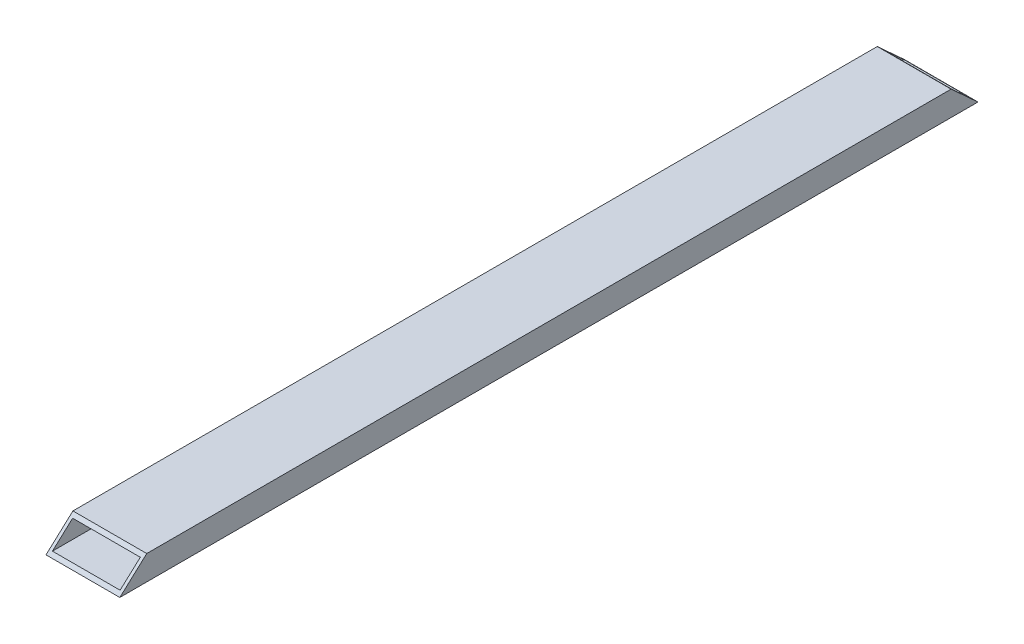
SolidWorks part; units mm, degrees
material "6063-T6"
ref_plane "Front Plane" through (0, 0, 0) normal (0, 0, 1) x (1, 0, 0)
ref_plane "Top Plane" through (0, 0, 0) normal (0, 1, 0) x (1, 0, 0)
ref_plane "Right Plane" through (0, 0, 0) normal (1, 0, 0) x (0, 0, -1)
sketch "Sketch1" plane through (0, 0, 0) normal (0, 0, 1) x (1, 0, 0)
  line L0 (-38.1, 0) -> (38.1, 0) construction
  line L1 (0, -12.7) -> (0, 12.7) construction
  line L2 (34.925, 0) -> (34.925, 9.525) construction
  line L3 (-38.1, -12.7) -> (38.1, -12.7) construction
  line L4 (-38.1, -12.7) -> (-38.1, 12.7) construction
  line L5 (-38.1, 12.7) -> (38.1, 12.7) construction
  line L6 (38.1, -12.7) -> (38.1, 12.7) construction
  line L7 (-38.1, -12.7) -> (38.1, 12.7) construction
  line L8 (-38.1, 12.7) -> (38.1, -12.7) construction
  line L9 (34.925, 9.525) -> (-34.925, 9.525) construction
  line L10 (-34.925, 9.525) -> (-34.925, -9.525) construction
  line L11 (-34.925, -9.525) -> (34.925, -9.525) construction
  line L12 (34.925, -9.525) -> (34.925, 0) construction
  point P0 (0, 0)
  point P4 (0, 0)
  point P9 (0, 0)
  point P10 (34.925, 0)
  point P13 (0, -9.525)
  point P14 (-34.925, 0)
  point P15 (0, 9.525)
  dimension "Width" = 76.2
  dimension "Wall Thickness" = 3.175
  dimension "Height" = 25.4
  dimension "D1" = 3.175
  dimension "D2" = 3.175
  dimension "D3" = 3.175
sketch "Sketch2" plane through (0, 0, 0) normal (1, 0, 0) x (0, 0, -1)
  line L0 (457.2, 12.7) -> (-457.2, 12.7) construction
  point P3 (-369.57, 12.7)
  point P5 (369.57, 12.7)
  point P7 (0, 12.7)
  dimension "D1" = 87.63
  dimension "D2" = 87.63
  dimension "Length" = 914.4
sketch "Sketch3" plane through (0, 0, 0) normal (0, 0, 1) x (1, 0, 0)
  line L1 (38.1, 12.7) -> (-38.1, 12.7)
  line L2 (-38.1, 12.7) -> (-38.1, -12.7)
  line L3 (-38.1, -12.7) -> (38.1, -12.7) construction
  line L4 (-38.1, -12.7) -> (38.1, -12.7)
  line L5 (38.1, -12.7) -> (38.1, 12.7)
  line L6 (-34.925, 9.525) -> (34.925, 9.525)
  line L7 (34.925, 9.525) -> (34.925, -9.525)
  line L8 (34.925, -9.525) -> (-34.925, -9.525)
  line L9 (-34.925, -9.525) -> (-34.925, 9.525)
extrude "Boss-Extrude1" add sketch "Sketch3" along normal mid plane 914.4
sketch "Sketch4" plane through (38.1, 0, 0) normal (1, 0, 0) x (0, 0, -1)
  line L0 (-457.2, -12.7) -> (457.2, -12.7) construction
  line L1 (442.9125, 12.7) -> (-442.9125, 12.7)
  line L2 (442.9125, 12.7) -> (442.9125, -12.7)
  line L3 (442.9125, -12.7) -> (-442.9125, -12.7)
  line L4 (-442.9125, 12.7) -> (-442.9125, -12.7)
  line L5 (442.9125, 12.7) -> (-442.9125, -12.7) construction
  line L6 (442.9125, -12.7) -> (-442.9125, 12.7) construction
  line L7 (0, 252.2904) -> (0, -470.7583) construction
  line L8 (-415.1312, 12.7) -> (-442.9125, -12.7)
  line L9 (415.1312, 12.7) -> (442.9125, -12.7)
  point P0 (0, 0)
  point P9 (-415.1312, 12.7)
  line M7 (457.2, -12.7) -> (457.2, 12.7)
  line M8 (457.2, 12.7) -> (-457.2, 12.7)
  line M9 (-457.2, 12.7) -> (-457.2, -12.7)
  line M10 (-457.2, -12.7) -> (457.2, -12.7)
  dimension "D1" = 885.825
  dimension "D2" = 415.1313
extrude "Cut-Extrude1" cut sketch "Sketch4" against normal through all contours L4 M8 M9 M10 | L8 L1 L4 | L2 M8 M10 M7 | L9 L2 M8
equation "\"D1@Boss-Extrude1\" = \"Length@Sketch2\""
equation "\"D1@Sketch2\" = \"Width@Sketch1\" * 1.15"
equation "\"D2@Sketch2\"=\"D1@Sketch2\""
equation "\"D1@Sketch1\"=\"Wall Thickness@Sketch1\""
equation "\"D2@Sketch1\"=\"Wall Thickness@Sketch1\""
equation "\"D3@Sketch1\"=\"Wall Thickness@Sketch1\""
